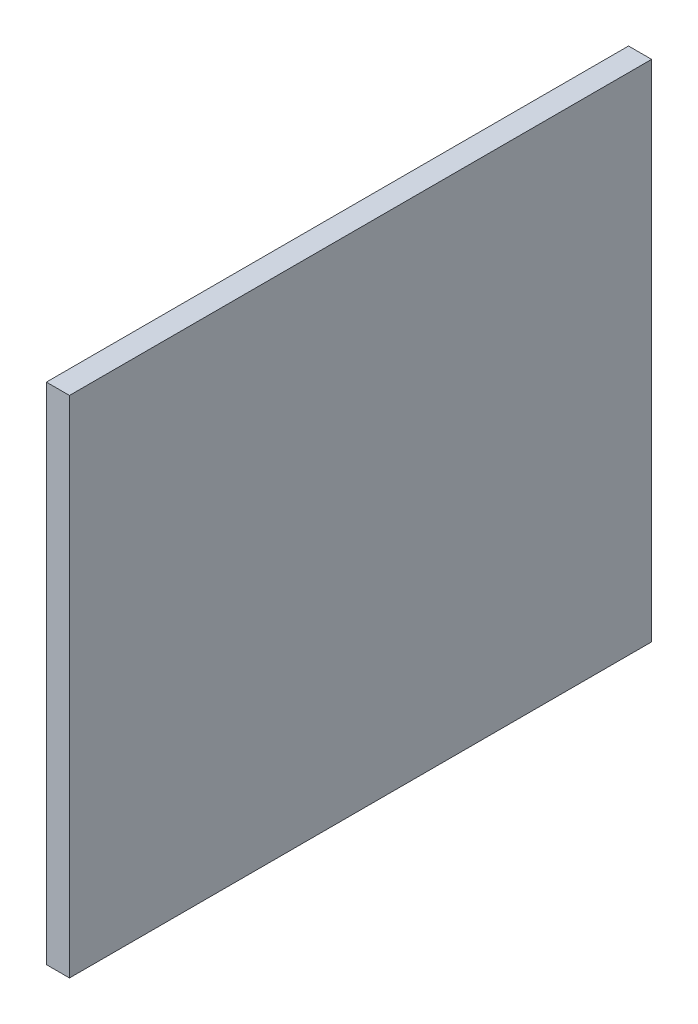
SolidWorks part; units mm, degrees
material "Oak"
ref_plane "Front Plane" through (0, 0, 0) normal (0, 0, 1) x (1, 0, 0)
ref_plane "Top Plane" through (0, 0, 0) normal (0, 1, 0) x (1, 0, 0)
ref_plane "Right Plane" through (0, 0, 0) normal (1, 0, 0) x (0, 0, -1)
sketch "Sketch1" plane through (0, 0, 0) normal (1, 0, 0) x (0, 0, -1)
  line L1 (-60, -52) -> (60, -52)
  line L2 (-60, -52) -> (-60, 52)
  line L3 (-60, 52) -> (60, 52)
  line L4 (60, -52) -> (60, 52)
  line L5 (-60, -52) -> (60, 52) construction
  line L6 (-60, 52) -> (60, -52) construction
  point P1 (0, 0)
  dimension "D1" = 104
  dimension "D2" = 120
extrude "Boss-Extrude1" add sketch "Sketch1" along normal blind 4.7625
